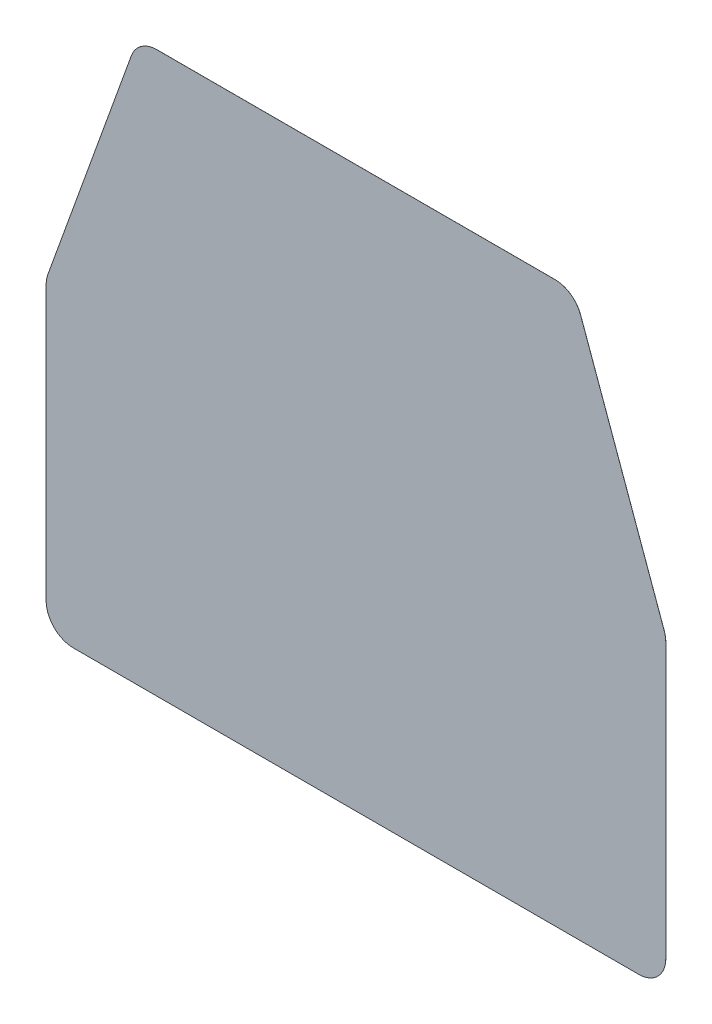
SolidWorks part; units mm, degrees
ref_plane "Front Plane" through (0, 0, 0) normal (0, 0, 1) x (1, 0, 0)
ref_plane "Top Plane" through (0, 0, 0) normal (0, 1, 0) x (1, 0, 0)
ref_plane "Right Plane" through (0, 0, 0) normal (1, 0, 0) x (0, 0, -1)
sketch "Sketch1" plane through (0, 0, 0) normal (0, 0, 1) x (1, 0, 0)
  line L0 (-132.08, 0) -> (132.08, 0)
  line L2 (93.0275, 261.62) -> (-93.0275, 261.62)
  line L3 (-104.9725, 253.2336) -> (-144.025, 145.0927)
  line L4 (-144.78, 140.7791) -> (-144.78, 12.7)
  line L5 (104.9725, 253.2336) -> (144.025, 145.0927)
  line L6 (144.78, 140.7791) -> (144.78, 12.7)
  line L7 (0, 0) -> (0, 261.62) construction
  arc A0 (-132.08, 0) -> (-144.78, 12.7) centre (-132.08, 12.7) cw
  arc A1 (144.78, 12.7) -> (132.08, 0) centre (132.08, 12.7) cw
  arc A2 (-144.025, 145.0927) -> (-144.78, 140.7791) centre (-132.08, 140.7791) ccw
  arc A3 (144.025, 145.0927) -> (144.78, 140.7791) centre (132.08, 140.7791) cw
  arc A4 (104.9725, 253.2336) -> (93.0275, 261.62) centre (93.0275, 248.92) ccw
  arc A5 (-93.0275, 261.62) -> (-104.9725, 253.2336) centre (-93.0275, 248.92) ccw
  point P11 (-144.78, 0)
  point P14 (144.78, 0)
  point P17 (-144.78, 143.002)
  point P24 (0, 0)
  point P26 (0, 0)
  dimension "D4" = 12.7
  dimension "D1" = 289.56
  dimension "D2" = 261.62
  dimension "D3" = 143.002
  dimension "D5" = 186.055
extrude "Boss-Extrude1" add sketch "Sketch1" along normal blind 0.0254
